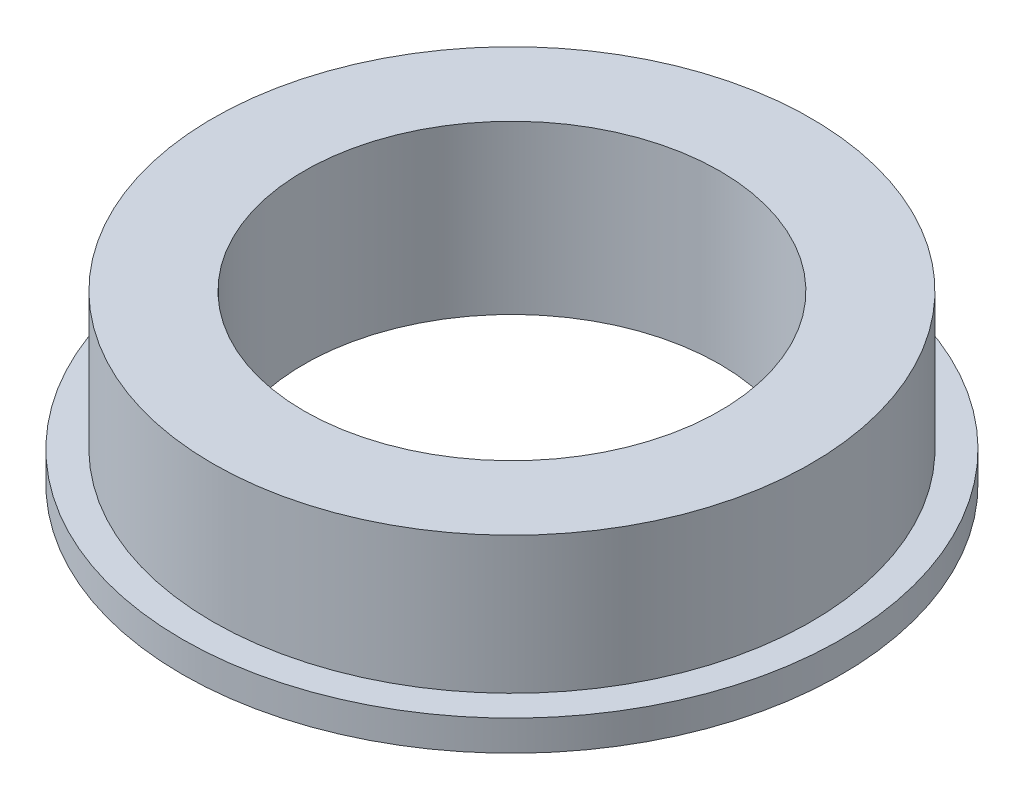
SolidWorks part; units mm, degrees
material "Cast Alloy Steel"
ref_plane "Front Plane" through (0, 0, 0) normal (0, 0, 1) x (1, 0, 0)
ref_plane "Top Plane" through (0, 0, 0) normal (0, 1, 0) x (1, 0, 0)
ref_plane "Right Plane" through (0, 0, 0) normal (1, 0, 0) x (0, 0, -1)
sketch "Sketch1" plane through (0, 0, 0) normal (0, 0, 1) x (1, 0, 0)
  line L0 (0, 2.6347) -> (0, -2.6347) construction
  line L1 (4, 0) -> (4, 3.5) construction
  line L2 (4, 3.5) -> (6, 3.5) construction
  line L3 (6, 3.5) -> (6, 0.8) construction
  line L4 (6, 0.8) -> (6.6, 0.8) construction
  line L5 (6.6, 0.8) -> (6.6, 0) construction
  line L6 (6.6, 0) -> (4, 0) construction
  line L7 (4.1, 0.1) -> (4.1, 3.4)
  line L8 (4.1, 3.4) -> (5.9, 3.4)
  line L9 (5.9, 3.4) -> (5.9, 0.7)
  line L10 (5.9, 0.7) -> (6.5, 0.7)
  line L11 (6.5, 0.7) -> (6.5, 0.1)
  line L12 (6.5, 0.1) -> (4.1, 0.1)
  point P4 (0, 0)
  dimension "D1" = 4
  dimension "D2" = 6
  dimension "D3" = 3.5
  dimension "D4" = 13.2
  dimension "D5" = 0.8
  dimension "D6" = 0.1
revolve "Revolve1" add sketch "Sketch1" angle 360 about L0
